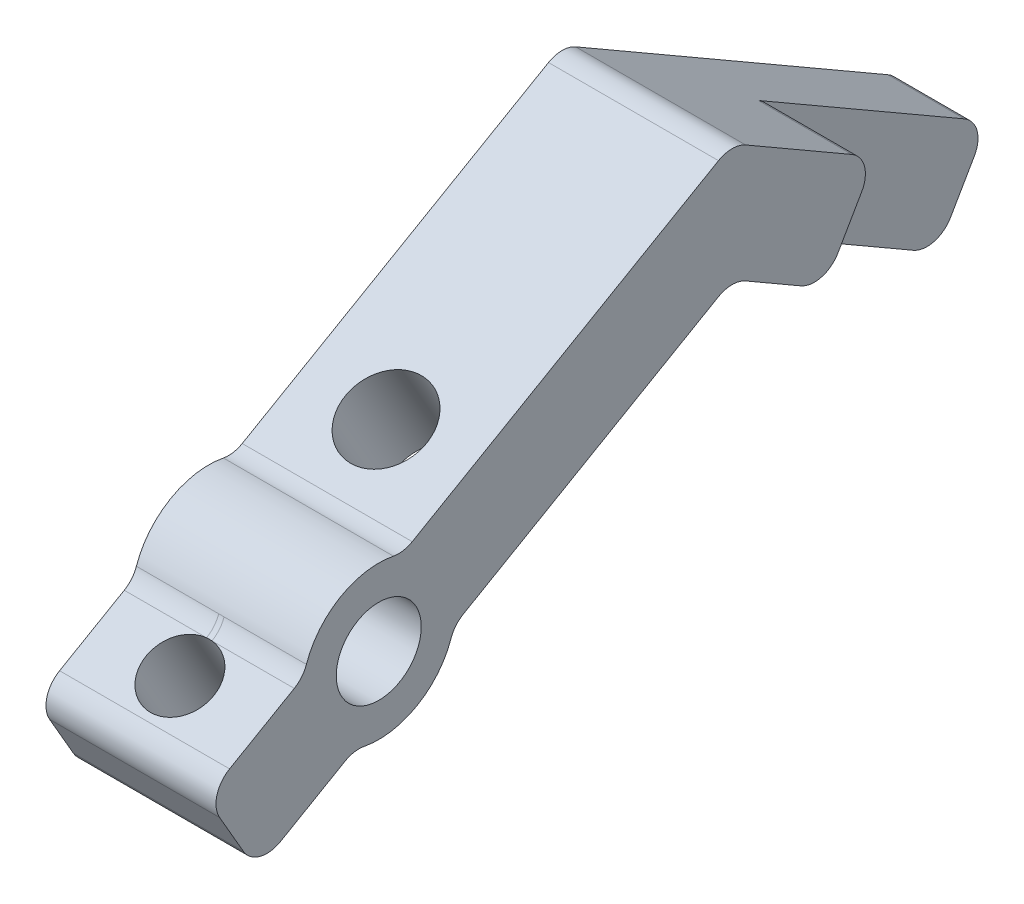
SolidWorks part; units mm, degrees
ref_plane "Front Plane" through (0, 0, 0) normal (0, 0, 1) x (1, 0, 0)
ref_plane "Top Plane" through (0, 0, 0) normal (0, 1, 0) x (1, 0, 0)
ref_plane "Right Plane" through (0, 0, 0) normal (1, 0, 0) x (0, 0, -1)
sketch "Sketch1" plane through (0, 0, 0) normal (1, 0, 0) x (0, 0, -1)
  line L0 (0, 19.05) -> (0, -19.05) construction
  line L1 (0, 19.05) -> (32.9956, 38.1) construction
  line L2 (32.9956, 38.1) -> (63.2415, 20.6375) construction
  line L3 (-8.2489, -14.2875) -> (2.1176, -8.6707) construction
  line L4 (-8.2489, -14.2875) -> (-13.7482, -11.1125) construction
  line L5 (0, 19.05) -> (-8.2489, 14.2875) construction
  line L6 (0, -19.05) -> (-8.2489, -14.2875) construction
  line L7 (10.9985, 25.4) -> (10.9985, -25.4) construction
  line L8 (-8.2489, 14.2875) -> (2.1176, 8.6707) construction
  line L9 (0, 0.3175) -> (-13.3728, 0.3175) construction
  line L10 (32.9956, -38.1) -> (63.2415, -20.6375) construction
  line L11 (0, -0.3175) -> (-13.3728, -0.3175) construction
  line L12 (-8.2489, 14.2875) -> (-13.7482, 11.1125) construction
  line L13 (32.9956, 43.5993) -> (-16.1294, 15.2369)
  line L14 (-16.1294, 15.2369) -> (-11.3669, 6.9881)
  line L15 (-11.3669, 6.9881) -> (32.9956, 32.6007)
  line L17 (0, 0) -> (-16.8904, 0) construction
  line L18 (-11.3669, -6.9881) -> (32.9956, -32.6007)
  line L20 (32.9956, -43.5993) -> (-16.1294, -15.2369)
  line L21 (-16.1294, -15.2369) -> (-11.3669, -6.9881)
  line L22 (32.9956, 43.5993) -> (65.6228, 24.7619)
  line L23 (65.6228, 24.7619) -> (60.8603, 16.5131)
  line L24 (60.8603, 16.5131) -> (32.9956, 32.6007)
  line L25 (32.9956, -43.5993) -> (65.6228, -24.7619)
  line L26 (65.6228, -24.7619) -> (60.8603, -16.5131)
  line L27 (60.8603, -16.5131) -> (32.9956, -32.6007)
  line L28 (0, -19.05) -> (32.9956, -38.1) construction
  circle A2 centre (0, 4.7625) radius 3.175 construction
  circle A3 centre (0, -4.7625) radius 3.175 construction
  arc A4 (2.1176, 8.6707) -> (0, 0.3175) centre (0, 4.7625) cw construction
  arc A5 (2.1176, -8.6707) -> (0, -0.3175) centre (0, -4.7625) ccw construction
  circle A6 centre (28.8658, 0) radius 12.7 construction
  circle A7 centre (0, 19.05) radius 3.9687
  circle A8 centre (0, 19.05) radius 7.1437
  circle A9 centre (0, -19.05) radius 7.1437
  circle A10 centre (0, -19.05) radius 3.9687
  point P0 (0, 0)
  dimension "D10" = 6.35
  dimension "D13" = 1.27
  dimension "D15" = 9.525
  dimension "D16" = 25.4
  dimension "D17" = 7.9375
  dimension "D18" = 14.2875
  dimension "D1" = 38.1
  dimension "D3" = 120
  dimension "D4" = 34.925
  dimension "D5" = 38.1
  dimension "D7" = 9.525
  dimension "D8" = 12.7
  dimension "D11" = 4.7625
  dimension "D14" = 6.35
  dimension "D19" = 30
extrude "Boss-Extrude1" add sketch "Sketch1" along normal blind 15.875 contours A8 L13 L14 L15 | L13 A8 | L15 A8 | A8 L15 L24 L23 L22 L13 | L13 A8 L15 A7
sketch "Sketch2" plane through (0, 18.4119, 10.6301) normal (0, 0.866, 0.5) x (1, 0, 0)
  line L0 (15.875, 5.5562) -> (15.875, 13.4937) construction
  line L1 (15.875, 5.5562) -> (15.875, 13.4937)
  line L2 (15.875, -6.35) -> (0, -6.35) construction
  circle A0 centre (7.9375, 0) radius 3.175
  circle A1 centre (7.9375, 22.225) radius 3.81
  point P4 (15.875, 9.525)
  point P5 (7.9375, -6.35)
  dimension "D1" = 6.35
  dimension "D3" = 7.62
  dimension "D2" = 9.525
  dimension "D4" = 12.7
extrude "Cut-Extrude1" cut sketch "Sketch2" against normal up to surface (9.525 mm away) contours A0 | A1 up to face at (7.9375, 25.0943, -19.994)
ref_plane "Plane2" through (15.875, 0, 0) normal (1, 0, 0) x (0, 0, -1)
sketch "Sketch3" plane through (15.875, 0, 0) normal (1, 0, 0) x (0, 0, -1)
  line L0 (65.6228, 24.7619) -> (60.8603, 16.5131) construction
  line L1 (32.9956, 43.5993) -> (65.6228, 24.7619) construction
  line L2 (60.8603, 16.5131) -> (32.9956, 32.6007) construction
  line L3 (65.6228, 24.7619) -> (60.8603, 16.5131)
  line L4 (46.3753, 35.8744) -> (65.6228, 24.7619)
  line L5 (60.8603, 16.5131) -> (41.6128, 27.6256)
  line L7 (41.6128, 27.6256) -> (46.3753, 35.8744)
  dimension "D1" = 22.225
extrude "Cut-Extrude2" cut sketch "Sketch3" against normal blind 8.7312
fillet "Fillet1" radius 2.54 12 edges at (7.9375, 17.5879, -6.9925) (7.9375, 12.2632, 2.23) (7.9375, 20.5121, 6.9925) (7.9375, 25.8368, -2.23) (7.9375, 43.5993, -32.9956) (7.9375, 32.6007, -32.9956) (3.5719, 24.7619, -65.6228) (3.5719, 16.5131, -60.8603) (7.9375, 15.2369, 16.1294) (7.9375, 6.9881, 11.3669) (11.5094, 35.8744, -46.3753) (11.5094, 27.6256, -41.6128)
